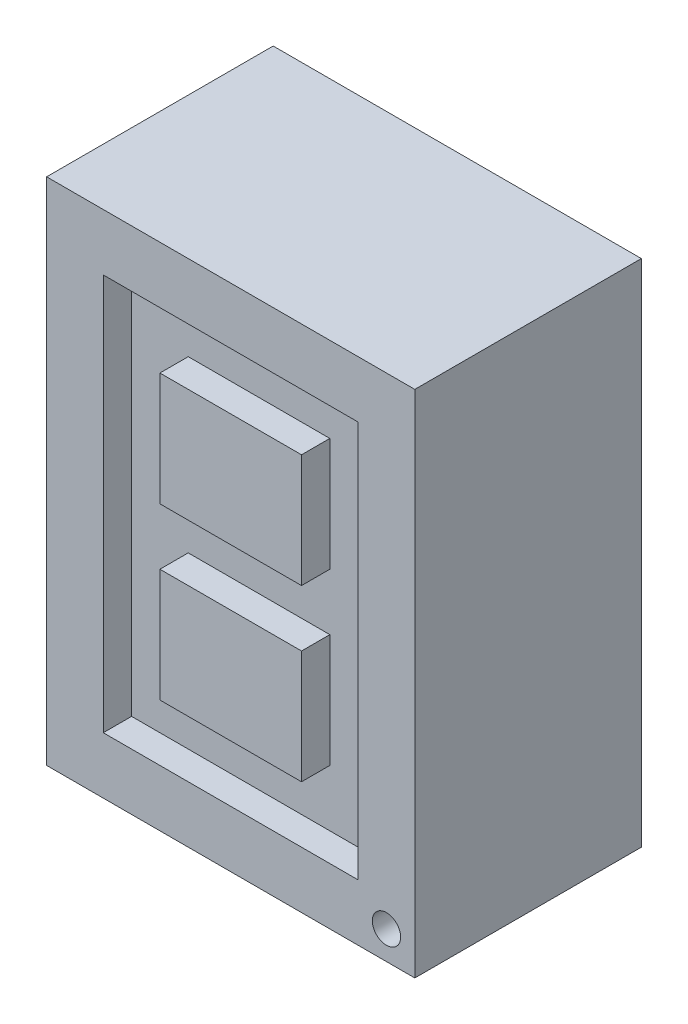
SolidWorks part; units mm, degrees
ref_plane "Plan de face" through (0, 0, 0) normal (0, 0, 1) x (1, 0, 0)
ref_plane "Plan de dessus" through (0, 0, 0) normal (0, 1, 0) x (1, 0, 0)
ref_plane "Plan de droite" through (0, 0, 0) normal (1, 0, 0) x (0, 0, -1)
sketch "Esquisse1" plane through (0, 0, 0) normal (0, 0, 1) x (1, 0, 0)
  line L1 (0, 0) -> (13, 0)
  line L2 (0, 0) -> (0, 18)
  line L3 (0, 18) -> (13, 18)
  line L4 (13, 0) -> (13, 18)
  dimension "D1" = 13
  dimension "D2" = 18
extrude "Boss.-Extru.1" add sketch "Esquisse1" along normal blind 8
sketch "Esquisse2" plane through (0, 0, 8) normal (0, 0, 1) x (1, 0, 0)
  line L0 (4, 14) -> (9, 14)
  line L3 (9, 14) -> (9, 10)
  line L4 (9, 4) -> (4, 4)
  line L5 (4, 4) -> (4, 8)
  line L6 (13, 18) -> (0, 18) construction
  line L7 (13, 0) -> (13, 18) construction
  line L8 (2, 16) -> (11, 16)
  line L9 (11, 16) -> (11, 2)
  line L10 (11, 2) -> (2, 2)
  line L11 (2, 2) -> (2, 16)
  line L12 (4, 10) -> (9, 10)
  line L13 (4, 8) -> (9, 8)
  line L14 (6.5, 10) -> (6.5, 8) construction
  line L15 (4, 10) -> (4, 14)
  line L16 (9, 8) -> (9, 4)
  line L17 (4, 4) -> (4, 14) construction
  line L18 (0, 0) -> (13, 0) construction
  line L19 (9, 14) -> (9, 4) construction
  circle A0 centre (12, 1) radius 0.5
  point P8 (6.5, 14)
  point P9 (6.5, 18)
  point P10 (2, 9)
  point P11 (13, 9)
  point P22 (6.5, 9)
  point P23 (11, 9)
  dimension "D7" = 1
  dimension "D1" = 4
  dimension "D2" = 4
  dimension "D4" = 2
  dimension "D5" = 1
  dimension "D6" = 1
  dimension "D3" = 2
extrude "Enlèv. mat.-Extru.1" cut sketch "Esquisse2" against normal blind 1
